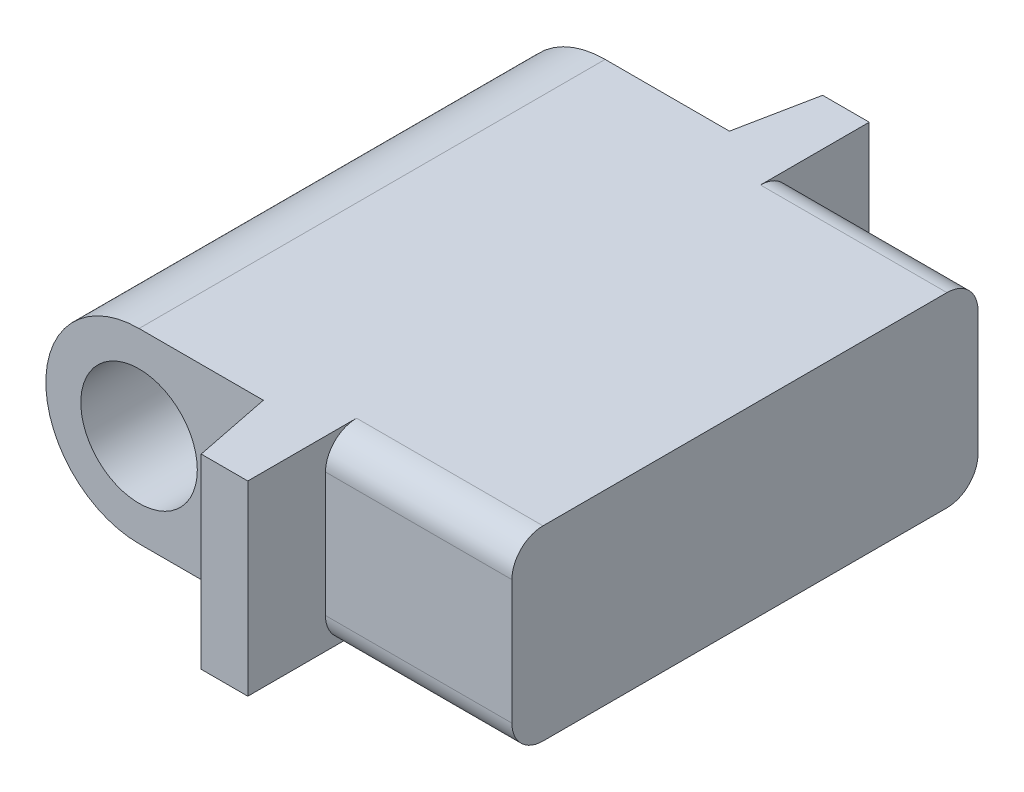
SolidWorks part; units mm, degrees
material "PTFE (general)"
ref_plane "Front Plane" through (0, 0, 0) normal (0, 0, 1) x (1, 0, 0)
ref_plane "Top Plane" through (0, 0, 0) normal (0, 1, 0) x (1, 0, 0)
ref_plane "Right Plane" through (0, 0, 0) normal (1, 0, 0) x (0, 0, -1)
sketch "Sketch1" plane through (0, 0, 0) normal (0, 1, 0) x (1, 0, 0)
  line L1 (19.05, -25.4) -> (-19.05, -25.4)
  line L2 (19.05, -25.4) -> (19.05, 25.4)
  line L3 (19.05, 25.4) -> (-19.05, 25.4)
  line L4 (-19.05, -25.4) -> (-19.05, 25.4)
  line L5 (19.05, -25.4) -> (-19.05, 25.4) construction
  line L6 (19.05, 25.4) -> (-19.05, -25.4) construction
  point P0 (0, 0)
  dimension "D1" = 38.1
  dimension "D2" = 50.8
extrude "Boss-Extrude1" add sketch "Sketch1" along normal blind 15.24
sketch "Sketch2" plane through (0, 15.24, 0) normal (0, 1, 0) x (1, 0, 0)
  line L0 (-19.05, 0) -> (19.05, 0) construction
  line L1 (-19.05, 25.4) -> (-1.27, 25.4)
  line L2 (-19.05, 25.4) -> (-19.05, 19.05)
  line L3 (-19.05, 19.05) -> (-1.27, 19.05)
  line L4 (-1.27, 25.4) -> (-1.27, 19.05)
  line L5 (-19.05, 25.4) -> (-19.05, -25.4) construction
  line L6 (19.05, -25.4) -> (19.05, 25.4) construction
  line L7 (-1.27, 19.05) -> (0, 25.4)
  line L8 (19.05, 25.4) -> (-19.05, 25.4) construction
  line L9 (0, 25.4) -> (3.81, 25.4)
  line L10 (3.81, 25.4) -> (3.81, 19.05)
  line L11 (3.81, 19.05) -> (19.05, 19.05)
  line L12 (3.81, -19.05) -> (19.05, -19.05)
  line L13 (3.81, -25.4) -> (3.81, -19.05)
  line L14 (0, -25.4) -> (3.81, -25.4)
  line L15 (-1.27, -19.05) -> (0, -25.4)
  line L16 (-1.27, -25.4) -> (-1.27, -19.05)
  line L17 (-19.05, -19.05) -> (-1.27, -19.05)
  line L18 (-19.05, -25.4) -> (-19.05, -19.05)
  line L19 (-19.05, -25.4) -> (-1.27, -25.4)
  point P11 (0, 25.4)
  line M7 (-19.05, 25.4) -> (-19.05, -25.4)
  line M8 (-19.05, -25.4) -> (19.05, -25.4)
  line M9 (19.05, -25.4) -> (19.05, 25.4)
  line M10 (19.05, 25.4) -> (-19.05, 25.4)
  dimension "D1" = 17.78
  dimension "D2" = 6.35
  dimension "D3" = 3.81
  dimension "D4" = 5.08
extrude "Cut-Extrude1" cut sketch "Sketch2" against normal blind 15.24 contours L4 L3 M10 M7 | L10 L11 M9 M10 | L17 L16 M7 M8 | L13 L12 M8 M9 | L16 L15 M8 | L4 L7 M10
sketch "Sketch3" plane through (0, 0, 19.05) normal (0, 0, 1) x (1, 0, 0)
  line L0 (-19.05, 0) -> (-19.05, 15.24) construction
  line L1 (-19.05, 0) -> (-1.27, 0) construction
  line L2 (-19.05, 15.24) -> (-1.27, 15.24) construction
  line L3 (-11.43, 15.24) -> (-19.05, 15.24)
  line L4 (-19.05, 15.24) -> (-19.05, 0)
  line L5 (-19.05, 0) -> (-11.43, 0)
  circle A0 centre (-11.43, 7.62) radius 7.62
  circle A1 centre (-11.43, 7.62) radius 4.7625
  line M1 (-1.27, 15.24) -> (-19.05, 15.24)
  line M2 (-19.05, 15.24) -> (-19.05, 0)
  line M3 (-19.05, 0) -> (-1.27, 0)
  dimension "D1" = 9.525
extrude "Cut-Extrude2" cut sketch "Sketch3" against normal through all contours A0 M1 M2 | A0 L4 M3 | A1
fillet "Fillet1" radius 2.54 4 edges at (11.43, 15.24, -19.05) (11.43, 0, -19.05) (11.43, 0, 19.05) (11.43, 15.24, 19.05)
